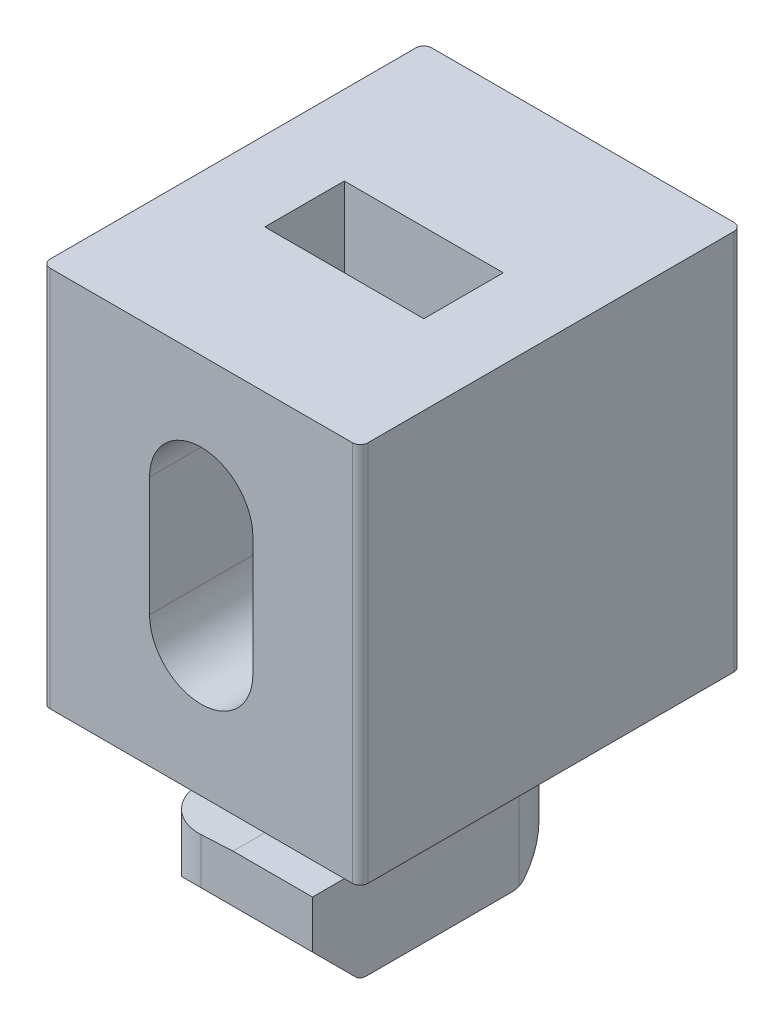
SolidWorks part; units mm, degrees
ref_plane "前视基准面" through (0, 0, 0) normal (0, 0, 1) x (1, 0, 0)
ref_plane "上视基准面" through (0, 0, 0) normal (0, 1, 0) x (1, 0, 0)
ref_plane "右视基准面" through (0, 0, 0) normal (1, 0, 0) x (0, 0, -1)
sketch "草图1" plane through (0, 0, 0) normal (0, 0, 1) x (1, 0, 0)
  line L1 (0, 0) -> (20, 0)
  line L2 (0, 0) -> (0, 24)
  line L3 (0, 24) -> (20, 24)
  line L4 (20, 0) -> (20, 24)
  dimension "D1" = 20
  dimension "D2" = 24
extrude "拉伸1" add sketch "草图1" along normal blind 24
sketch "草图2" plane through (0, 0, 24) normal (0, 0, 1) x (1, 0, 0)
  line L0 (6.75, 15.75) -> (6.75, 8.25)
  line L1 (13.25, 15.75) -> (13.25, 8.25)
  line L2 (0, 24) -> (0, 0) construction
  line L3 (20, 24) -> (0, 24) construction
  arc A0 (6.75, 15.75) -> (13.25, 15.75) centre (10, 15.75) cw
  arc A1 (6.75, 8.25) -> (13.25, 8.25) centre (10, 8.25) ccw
  dimension "D3" = 7.5
  dimension "D4" = 7.5
  dimension "D6" = 8.25
  dimension "D1" = 6.5
  dimension "D2" = 6.75
  dimension "D5" = 8.25
  dimension "D7" = 8.25
extrude "切除-拉伸1" cut sketch "草图2" against normal blind 24
sketch "草图3" plane through (0, 24, 0) normal (0, 1, 0) x (1, 0, 0)
  line L0 (0, -24) -> (0, 0) construction
  line L1 (5, -10) -> (15, -10)
  line L2 (5, -10) -> (5, -15)
  line L3 (5, -15) -> (15, -15)
  line L4 (15, -10) -> (15, -15)
  line L5 (20, -24) -> (0, -24) construction
  dimension "D1" = 10
  dimension "D2" = 5
  dimension "D3" = 5
  dimension "D4" = 9
extrude "切除-拉伸2" cut sketch "草图3" against normal blind 20
sketch "草图4" plane through (0, 0, 0) normal (0, -1, 0) x (1, 0, 0)
  line L0 (15, 19) -> (10, 19)
  line L1 (0, 24) -> (0, 0) construction
  line L2 (0, 24) -> (20, 24) construction
  line L5 (15, 19) -> (15, 14)
  line L6 (5, 9) -> (10, 9)
  line L7 (5, 9) -> (5, 14)
  arc A0 (10, 19) -> (5, 14) centre (10, 14) ccw
  arc A1 (10, 9) -> (15, 14) centre (10, 14) ccw
  dimension "D1" = 5
  dimension "D2" = 5
  dimension "D3" = 5
  dimension "D4" = 5
  dimension "D5" = 5
  dimension "D6" = 5
  dimension "D7" = 10
extrude "拉伸2" add sketch "草图4" along normal blind 10
sketch "草图5" plane through (0, -10, 0) normal (0, -1, 0) x (1, 0, 0)
  line L1 (5, 22) -> (15, 22)
  line L2 (5, 22) -> (5, 6)
  line L3 (5, 6) -> (15, 6)
  line L4 (15, 22) -> (15, 6)
  line L6 (0, 0) -> (20, 0) construction
  line L8 (20, 24) -> (20, 0) construction
  dimension "D1" = 16
  dimension "D2" = 10
  dimension "D3" = 5
  dimension "D4" = 6
extrude "拉伸3" add sketch "草图5" against normal blind 6
fillet "圆角2" radius 0.5 4 edges at (20, 12, 24) (0, 12, 0) (20, 12, 0) (0, 12, 24)
chamfer "倒角3" distance 3 angle 45 1 edges at (10, -10, 22)
chamfer "倒角4" distance 3 angle 45 1 edges at (10, -10, 6)
fillet "圆角3" radius 1 2 edges at (10, -10, 9) (10, -10, 19)
sketch "草图8" plane through (0, 0, 22) normal (0, 0, 1) x (1, 0, 0)
  line L0 (10, -4) -> (5, -4)
  line L1 (15, -4) -> (5, -4) construction
  line L2 (5, -4) -> (5, -4.262)
  line L4 (5, -4) -> (5, -7) construction
  line L5 (5, -4.262) -> (10, -4)
  dimension "D1" = 3
extrude "切除-拉伸3" cut sketch "草图8" against normal up to surface (8 mm away)
sketch "草图9" plane through (0, 0, 6) normal (0, 0, -1) x (-1, 0, 0)
  line L0 (-10, -4) -> (-15, -4)
  line L1 (-15, -4) -> (-15, -4.262)
  line L2 (-15, -4) -> (-15, -7) construction
  line L3 (-15, -4.262) -> (-10, -4)
  dimension "D1" = 3
extrude "切除-拉伸4" cut sketch "草图9" against normal up to surface (8 mm away)
fillet "圆角6" radius 3 1 edges at (15, -5.631, 6)
fillet "圆角7" radius 3 1 edges at (5, -5.631, 22)
